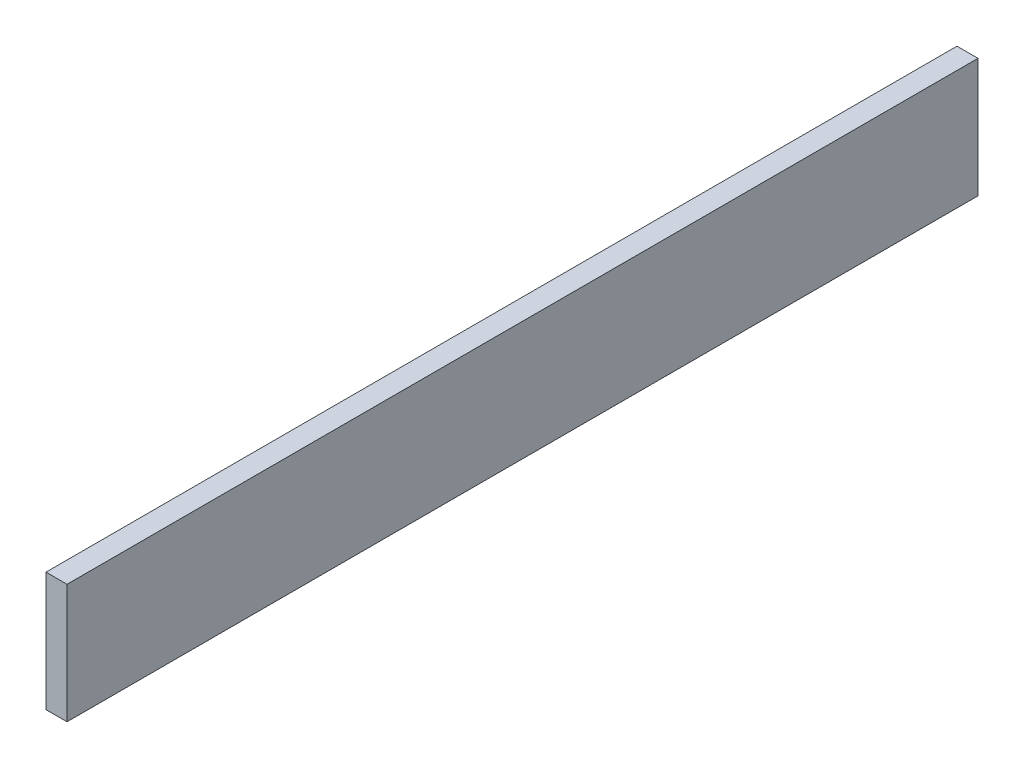
SolidWorks part; units mm, degrees
ref_plane "Front Plane" through (0, 0, 0) normal (0, 0, 1) x (1, 0, 0)
ref_plane "Top Plane" through (0, 0, 0) normal (0, 1, 0) x (1, 0, 0)
ref_plane "Right Plane" through (0, 0, 0) normal (1, 0, 0) x (0, 0, -1)
sketch "Sketch1" plane through (0, 0, 0) normal (1, 0, 0) x (0, 0, -1)
  line L1 (0, 0) -> (130, 0)
  line L2 (0, 0) -> (0, 17)
  line L3 (0, 17) -> (130, 17)
  line L4 (130, 0) -> (130, 17)
  dimension "D1" = 17
  dimension "D2" = 130
extrude "Boss-Extrude1" add sketch "Sketch1" along normal blind 3
